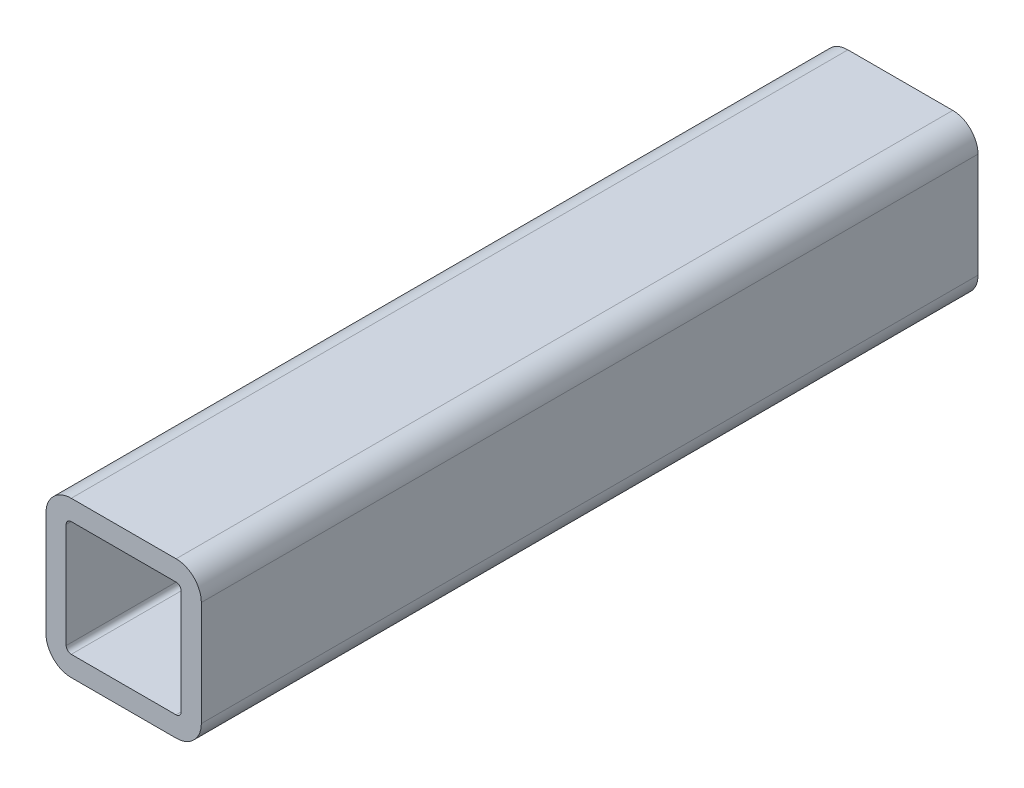
SolidWorks part; units mm, degrees
ref_plane "Front" through (0, 0, 0) normal (0, 0, 1) x (1, 0, 0)
ref_plane "Top" through (0, 0, 0) normal (0, 1, 0) x (1, 0, 0)
ref_plane "Right" through (0, 0, 0) normal (1, 0, 0) x (0, 0, -1)
sketch "Sketch1" plane through (0, 0, 0) normal (0, 0, 1) x (1, 0, 0)
  line L0 (-4.699, 0) -> (-6.35, 0) construction
  line L1 (4.2863, -6.35) -> (-4.2863, -6.35)
  line L2 (6.35, -4.2863) -> (6.35, 4.2863)
  line L3 (4.2863, 6.35) -> (-4.2863, 6.35)
  line L4 (-6.35, -4.2863) -> (-6.35, 4.2863)
  line L5 (6.35, -6.35) -> (-6.35, 6.35) construction
  line L6 (6.35, 6.35) -> (-6.35, -6.35) construction
  line L7 (4.2863, 4.699) -> (-4.2863, 4.699)
  line L8 (4.699, 4.2863) -> (4.699, -4.2863)
  line L9 (4.2863, -4.699) -> (-4.2863, -4.699)
  line L10 (-4.699, 4.2863) -> (-4.699, -4.2863)
  line L11 (4.699, 4.699) -> (-4.699, -4.699) construction
  line L12 (4.699, -4.699) -> (-4.699, 4.699) construction
  line L13 (0, -4.699) -> (0, -6.35) construction
  arc A0 (-4.2863, -4.699) -> (-4.699, -4.2863) centre (-4.2863, -4.2863) cw
  arc A1 (4.699, -4.2863) -> (4.2863, -4.699) centre (4.2863, -4.2863) cw
  arc A2 (4.2863, 4.699) -> (4.699, 4.2863) centre (4.2863, 4.2863) cw
  arc A3 (-4.2863, 4.699) -> (-4.699, 4.2863) centre (-4.2863, 4.2863) ccw
  arc A4 (4.2863, -6.35) -> (6.35, -4.2863) centre (4.2863, -4.2863) ccw
  arc A5 (6.35, 4.2863) -> (4.2863, 6.35) centre (4.2863, 4.2863) ccw
  arc A6 (-4.2863, 6.35) -> (-6.35, 4.2863) centre (-4.2863, 4.2863) ccw
  arc A7 (-4.2863, -6.35) -> (-6.35, -4.2863) centre (-4.2863, -4.2863) cw
  point P0 (0, 0)
  point P6 (0, 0)
  dimension "D4" = 2.0638
  dimension "Outside Width" = 12.7
  dimension "Ouside Height" = 12.7
  dimension "D5" = 1.651
  dimension "Inside Width" = 9.398
  dimension "Wall Thickness" = 1.651
sketch "Sketch2" plane through (0, 0, 0) normal (1, 0, 0) x (0, 0, -1)
  line L0 (-31.75, 0) -> (31.75, 0) construction
  line L1 (31.75, -6.35) -> (31.75, 6.35)
  line L2 (-31.75, -6.35) -> (-31.75, 6.35)
  line L3 (0, -6.35) -> (0, 6.35) construction
  point P3 (-20.6375, 0)
  point P6 (31.75, 0)
  point P9 (-31.75, 0)
  point P12 (0, 0)
  point P13 (20.6375, 0)
  dimension "D1" = 11.1125
  dimension "Length" = 63.5
sketch "Sketch4" plane through (0, 0, 0) normal (0, 0, 1) x (1, 0, 0)
  line L0 (6.35, -4.2863) -> (6.35, 4.2863) construction
  line L1 (4.2863, 6.35) -> (-4.2863, 6.35) construction
  line L2 (-6.35, -4.2863) -> (-6.35, 4.2863) construction
  line L3 (4.2863, -6.35) -> (-4.2863, -6.35) construction
  line L4 (4.699, 4.2863) -> (4.699, -4.2863) construction
  line L5 (4.2863, -4.699) -> (-4.2863, -4.699) construction
  line L6 (-4.699, 4.2863) -> (-4.699, -4.2863) construction
  line L7 (4.2863, 4.699) -> (-4.2863, 4.699) construction
  line L8 (6.35, -4.2863) -> (6.35, 4.2863)
  line L9 (4.2863, 6.35) -> (-4.2863, 6.35)
  line L10 (-6.35, -4.2863) -> (-6.35, 4.2863)
  line L11 (4.2863, -6.35) -> (-4.2863, -6.35)
  line L12 (4.699, 4.2863) -> (4.699, -4.2863)
  line L13 (4.2863, -4.699) -> (-4.2863, -4.699)
  line L14 (-4.699, 4.2863) -> (-4.699, -4.2863)
  line L15 (4.2863, 4.699) -> (-4.2863, 4.699)
  arc A0 (6.35, 4.2863) -> (4.2863, 6.35) centre (4.2863, 4.2863) ccw construction
  arc A1 (-4.2863, 6.35) -> (-6.35, 4.2863) centre (-4.2863, 4.2863) ccw construction
  arc A2 (-6.35, -4.2863) -> (-4.2863, -6.35) centre (-4.2863, -4.2863) ccw construction
  arc A3 (4.2863, -6.35) -> (6.35, -4.2863) centre (4.2863, -4.2863) ccw construction
  arc A4 (4.2863, -4.699) -> (4.699, -4.2863) centre (4.2863, -4.2863) ccw construction
  arc A5 (-4.699, -4.2863) -> (-4.2863, -4.699) centre (-4.2863, -4.2863) ccw construction
  arc A6 (-4.2863, 4.699) -> (-4.699, 4.2863) centre (-4.2863, 4.2863) ccw construction
  arc A7 (4.699, 4.2863) -> (4.2863, 4.699) centre (4.2863, 4.2863) ccw construction
  arc A8 (6.35, 4.2863) -> (4.2863, 6.35) centre (4.2863, 4.2863) ccw
  arc A9 (-4.2863, 6.35) -> (-6.35, 4.2863) centre (-4.2863, 4.2863) ccw
  arc A10 (-6.35, -4.2863) -> (-4.2863, -6.35) centre (-4.2863, -4.2863) ccw
  arc A11 (4.2863, -6.35) -> (6.35, -4.2863) centre (4.2863, -4.2863) ccw
  arc A12 (4.2863, -4.699) -> (4.699, -4.2863) centre (4.2863, -4.2863) ccw
  arc A13 (-4.699, -4.2863) -> (-4.2863, -4.699) centre (-4.2863, -4.2863) ccw
  arc A14 (-4.2863, 4.699) -> (-4.699, 4.2863) centre (-4.2863, 4.2863) ccw
  arc A15 (4.699, 4.2863) -> (4.2863, 4.699) centre (4.2863, 4.2863) ccw
extrude "Boss-Extrude1" add sketch "Sketch4" along normal mid plane 63.5
equation "\"D1@Sketch2\"=\"Outside Width@Sketch1\"*.875"
equation "\"D1@Boss-Extrude1\"=\"Length@Sketch2\""
equation "\"D4@Sketch1\"=\"D5@Sketch1\"*1.25"
